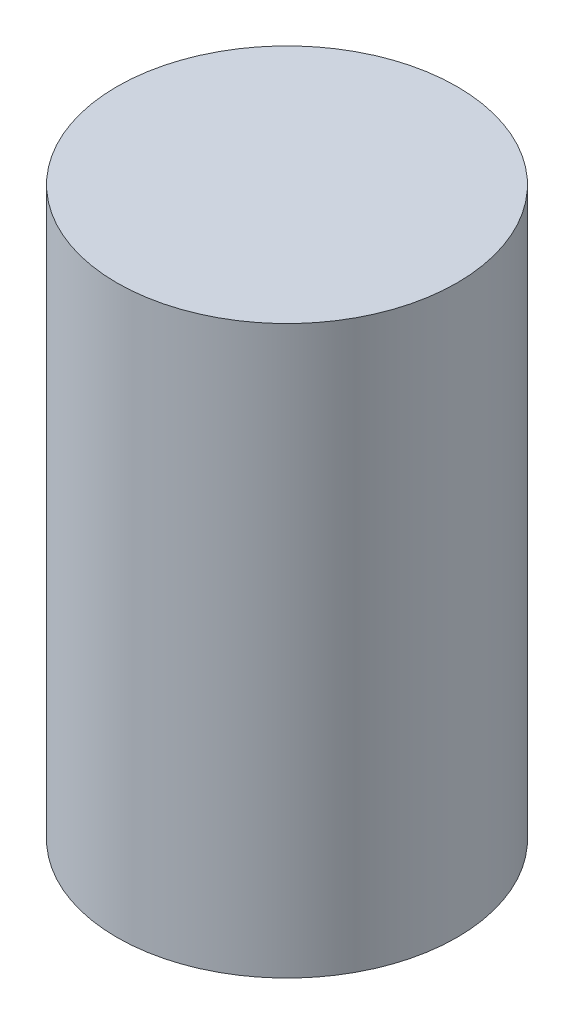
SolidWorks part; units mm, degrees
ref_plane "Ebene vorne" through (0, 0, 0) normal (0, 0, 1) x (1, 0, 0)
ref_plane "Ebene oben" through (0, 0, 0) normal (0, 1, 0) x (1, 0, 0)
ref_plane "Ebene rechts" through (0, 0, 0) normal (1, 0, 0) x (0, 0, -1)
sketch "Skizze1" plane through (0, 0, 0) normal (0, 1, 0) x (1, 0, 0)
  circle A0 centre (0, 0) radius 30
extrude "Aufsatz-Linear austragen1" add sketch "Skizze1" along normal blind 100
ref_plane "Testebene" through (30, 0, 0) normal (1, 0, 0) x (0, 0, -1)
sketch "Skizze4" plane through (30, 0, 0) normal (1, 0, 0) x (0, 0, -1)
  line L0 (30, 100) -> (-30, 100) construction
  spline S0 degree 3 poles (-27.6037, 100) (32.292, 91.193) (-60.7026, 27.0638) (31.1775, 24.8235) (24.904, 0) knots 0 0 0 0 0.548355 1 1 1 1
sketch "Skizze6" plane through (0, 0, 0) normal (1, 0, 0) x (0, 0, -1)
  spline S0 degree 3 poles (-1.2347, 100.5497) (-45.7943, 52.9816) (8.9058, 94.4544) (5.8155, 53.8506) (-39.9111, 55.6525) (41.3321, 15.5738) (17.0049, 3.9168) knots 0 0 0 0 0.339903 0.455081 0.572778 1 1 1 1
curve "Kurve2"
sketch "Skizze7" plane through (0, 0, 0) normal (0, -1, 0) x (1, 0, 0)
  line L0 (29.4609, -2.584) -> (30.3007, -2.584)
  line L1 (30.3007, -2.584) -> (30.3007, -1.8905)
  line L2 (30.3007, -1.8905) -> (29.4609, -1.8905)
  arc A0 (29.4609, -1.8905) -> (29.4609, -2.584) centre (29.4609, -2.2372) ccw
